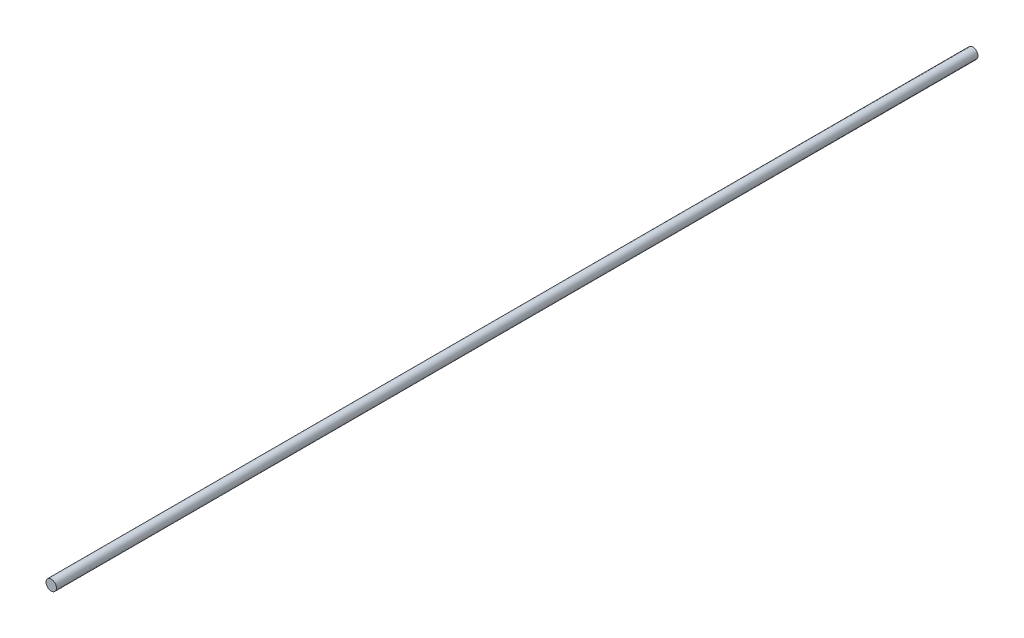
SolidWorks part; units mm, degrees
ref_plane "Plano frontal" through (0, 0, 0) normal (0, 0, 1) x (1, 0, 0)
ref_plane "Plano superior" through (0, 0, 0) normal (0, 1, 0) x (1, 0, 0)
ref_plane "Plano direito" through (0, 0, 0) normal (1, 0, 0) x (0, 0, -1)
ref_plane "Plano1" through (0, 0, 0) normal (0, -1, 0) x (1, 0, 0)
sketch "Esboço1" plane through (0, 0, 0) normal (0, -1, 0) x (1, 0, 0)
  line L0 (13, 2300) -> (0, 2300)
  line L1 (0, 2300) -> (0, 0)
  line L2 (0, 0) -> (13, 0)
  line L3 (13, 0) -> (13, 2300)
  line L4 (0, 2300) -> (0, 0) construction
  dimension "D1" = 13
  dimension "D2" = 2300
revolve "Revolução1" add sketch "Esboço1" angle 360 about L4
